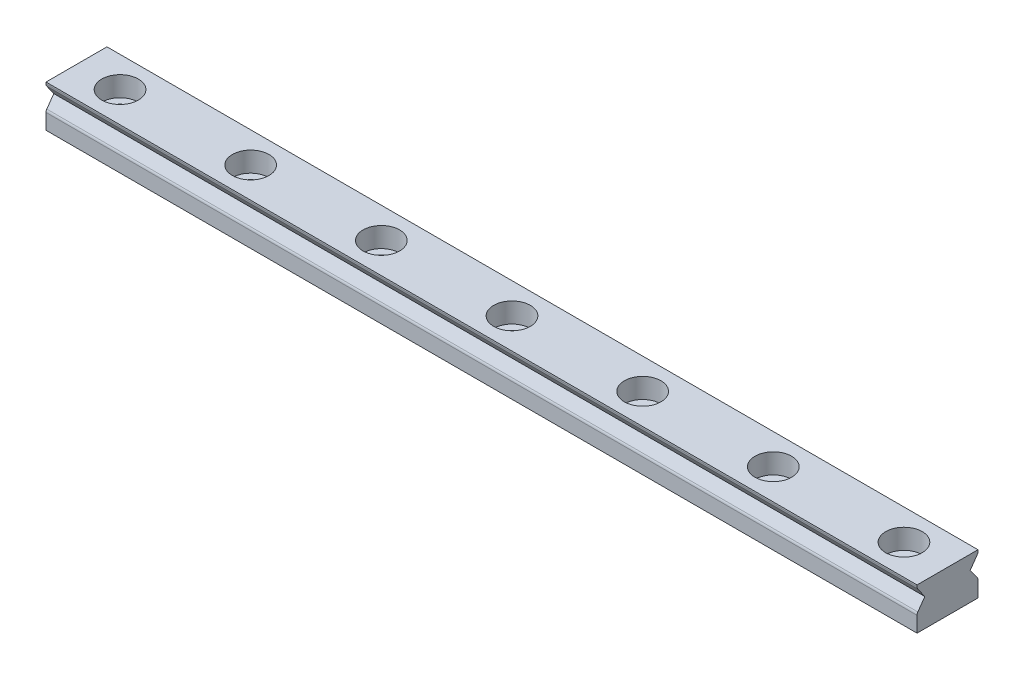
SolidWorks part; units mm, degrees
material "1060 合金"
ref_plane "前视基准面" through (0, 0, 0) normal (0, 0, 1) x (1, 0, 0)
ref_plane "上视基准面" through (0, 0, 0) normal (0, 1, 0) x (1, 0, 0)
ref_plane "右视基准面" through (0, 0, 0) normal (1, 0, 0) x (0, 0, -1)
sketch "草图1" plane through (0, 0, 0) normal (0, 0, 1) x (1, 0, 0)
  line L0 (-74.0142, 0) -> (81.6091, 0) construction
  line L1 (0, 43.2896) -> (0, -42.1937) construction
  line L3 (-50, 2.4) -> (50, 2.4)
  line L4 (-50, 2.4) -> (-50, -2.4)
  line L5 (-50, -2.4) -> (50, -2.4)
  line L6 (50, 2.4) -> (50, -2.4)
  dimension "D1" = 4.8
  dimension "D2" = 2.4
  dimension "D3" = 100
  dimension "D4" = 50
extrude "凸台-拉伸1" add sketch "草图1" along normal mid plane 7
sketch "草图3" plane through (0, 2.4, 0) normal (0, 1, 0) x (1, 0, 0)
  line L0 (-45, 3.5) -> (-45, -3.5) construction
  line L1 (50, 3.5) -> (-50, 3.5) construction
  line L2 (50, -3.5) -> (-50, -3.5) construction
  line L3 (-50, 0) -> (-10.5543, 0) construction
  line L4 (-50, -3.5) -> (-50, 3.5) construction
  circle A0 centre (-45, 0) radius 2.1
  dimension "D2" = 4.2
  dimension "D1" = 5
extrude "切除-拉伸1" cut sketch "草图3" against normal blind 2.3
sketch "草图4" plane through (0, 0.1, 0) normal (0, 1, 0) x (1, 0, 0)
  circle A0 centre (-45, 0) radius 1.2
  dimension "D1" = 2.4
extrude "切除-拉伸2" cut sketch "草图4" against normal up to next (2.5 mm away)
mirror "镜向1" about plane through (0, 0, 0) normal (1, 0, 0) of "切除-拉伸2", "切除-拉伸1"
sketch "草图6" plane through (-50, 0, 0) normal (-1, 0, 0) x (0, 0, 1)
  line L0 (3.4081, 1.935) -> (2.6045, 0.8)
  line L1 (3.5, 0.8) -> (-0.5115, 0.8) construction
  line L2 (2.6045, 0.8) -> (3.4081, -0.335)
  line L3 (3.5, 2.4) -> (3.5, -2.4) construction
  line L4 (3.4045, 1.9323) -> (3.4045, -0.903) construction
  line L6 (3.5, 2.4) -> (3.5, 2.2239)
  line L7 (3.5, -0.6239) -> (3.5, -2.4) construction
  arc A0 (3.5, 2.2239) -> (3.4081, 1.935) centre (3, 2.2239) cw
  arc A1 (3.5, -0.6239) -> (3.4081, -0.335) centre (3, -0.6239) ccw
  point P17 (3.5, -0.4648)
  dimension "D2" = 0.5
  dimension "D1" = 0.5
  dimension "D3" = 1.5
  dimension "D4" = 0.8
  dimension "D5" = 1.6
extrude "切除-拉伸4" cut sketch "草图6" against normal through all and the other way through all flip side to cut
mirror "镜向3" about plane through (0, 0, 0) normal (0, 0, 1) of "切除-拉伸4"
pattern_linear "阵列(线性)1" count 6 spacing 15 along (1, 0, 0) of "切除-拉伸1", "切除-拉伸2"
